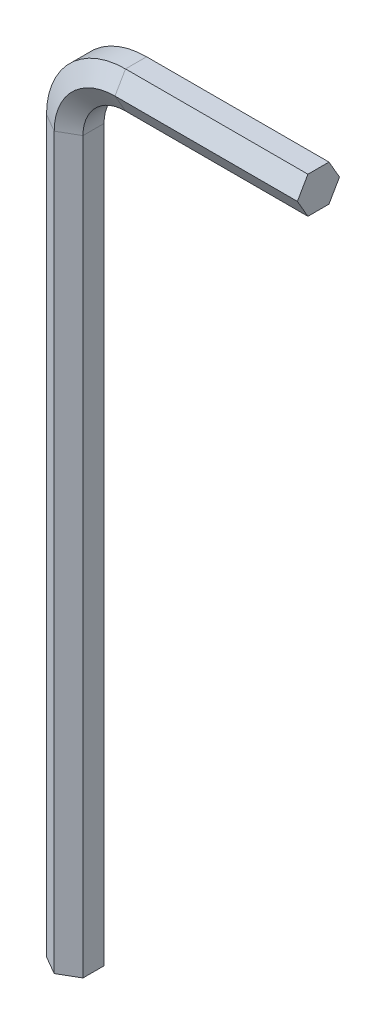
SolidWorks part; units mm, degrees
ref_plane "Přední rovina" through (0, 0, 0) normal (0, 0, 1) x (1, 0, 0)
ref_plane "Vrchní rovina" through (0, 0, 0) normal (0, 1, 0) x (1, 0, 0)
ref_plane "Pravá rovina" through (0, 0, 0) normal (1, 0, 0) x (0, 0, -1)
sketch "Skica1" plane through (0, 0, 0) normal (0, 0, 1) x (1, 0, 0)
  line L0 (0, 0) -> (0, 60)
  line L1 (5, 65) -> (20, 65)
  arc A0 (0, 60) -> (5, 65) centre (5, 60) cw
  dimension "D2" = 5
  dimension "D1" = 60
  dimension "D3" = 15
sketch "Skica2" plane through (0, 0, 0) normal (0, 1, 0) x (1, 0, 0)
  line L1 (1.5, 0.866) -> (0, 1.7321)
  line L2 (0, 1.7321) -> (-1.5, 0.866)
  line L3 (-1.5, 0.866) -> (-1.5, -0.866)
  line L4 (-1.5, -0.866) -> (0, -1.7321)
  line L5 (0, -1.7321) -> (1.5, -0.866)
  line L6 (1.5, -0.866) -> (1.5, 0.866)
  circle A0 centre (0, 0) radius 1.5 construction
  point P1 (1.5287, -0.8143)
  point P10 (0, 0)
  dimension "D1" = 3
sweep "Táhnout po křivce1" add profiles "Skica2" path "Skica1"
